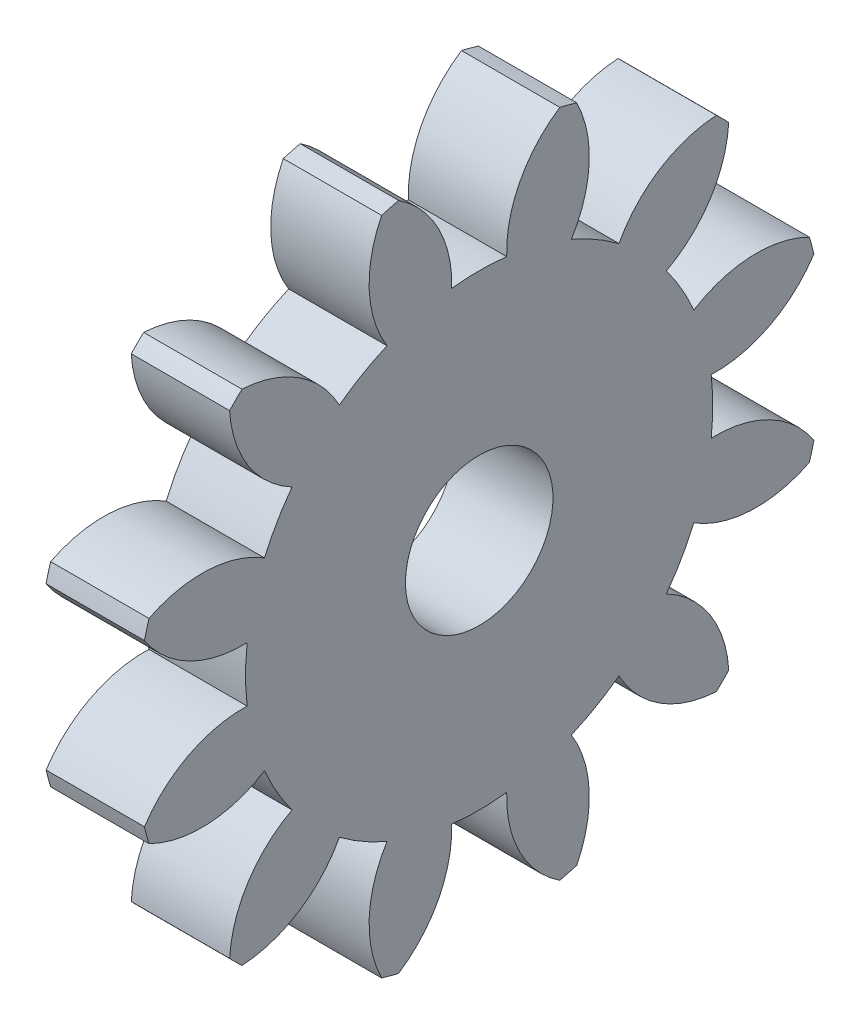
SolidWorks part; units mm, degrees
ref_plane "Plane1" through (0, 0, 0) normal (0, 0, 1) x (1, 0, 0)
ref_plane "Plane2" through (0, 0, 0) normal (0, 1, 0) x (1, 0, 0)
ref_plane "Plane3" through (0, 0, 0) normal (1, 0, 0) x (0, 0, -1)
sketch "HoldingSke" plane through (0, 0, 0) normal (0, 1, 0) x (1, 0, 0)
  line L0 (0, 0) -> (0.1534, -0.0354)
  line L1 (-15, 0) -> (100, 0) construction
  line L2 (0, 0) -> (-2.1039, 2.3779)
  line L3 (0, 0) -> (-11.863, 4.5341)
  line L4 (0, 0) -> (8.4473, 1.7955)
  line L5 (0, 0) -> (-23.7986, -8.8762)
  line L6 (0, 0) -> (-10.5278, -7.1032)
  line L7 (-2.1039, 2.3779) -> (3.3635, 27.1825)
  line L8 (-76.2, 54.61) -> (-73.66, 54.61)
  line L9 (-71.009, 38.7566) -> (-53.1078, 45.2721)
  line L10 (-76.2, 71.12) -> (104.1128, 71.12)
  line L11 (0, 0) -> (-12.7, 0)
  line L12 (-76.2, 101.6) -> (-75.9714, 101.6)
  line L13 (24.9733, 27.94) -> (52.9518, 28.4284)
  line L14 (24.9733, 27.94) -> (24.9746, 27.94)
  line L15 (24.9733, 27.94) -> (100.4006, 29.5858)
  line L16 (-63.627, -6.35) -> (-12.827, -6.35)
  circle A0 centre (0, 0) radius 9.525
  circle A1 centre (0, 0) radius 12.7
  circle A2 centre (0, 0) radius 12.7
  circle A3 centre (0, 0) radius 9.525
  dimension "Bore" = 19.05
  dimension "MBD" = 19.05
  dimension "T_dim" = 2.54
  dimension "Ap" = 20
  dimension "H" = 19.05
  dimension "Pitch_radius" = 180.3128
  dimension "Addendum_fac" = 1
  dimension "Dedendum_fac" = 1.25
  dimension "Clearance_fac" = 0.25
  dimension "Dedendum_add" = 0.0013
  dimension "Module" = 6.35
sketch "BasProSke" plane through (0, 0, 0) normal (0, 1, 0) x (1, 0, 0)
  line L0 (-10, 0) -> (60, 0) construction
  line L1 (0, 0) -> (0, 44.45)
  line L2 (0, 0) -> (12.7, 0)
  line L3 (12.7, 0) -> (12.7, 44.45)
  line L4 (12.7, 44.45) -> (0, 44.45)
revolve "Base-Revolve" add sketch "BasProSke" angle 360 about L0
sketch "TooCutSke" plane through (0, 0, 0) normal (1, 0, 0) x (0, 0, -1)
  line L1 (0, 0) -> (0, 107) construction
  line L2 (0, 0) -> (-5.3725, 37.7193) construction
  line L3 (0, 0) -> (-19.5794, 73.0714) construction
  line L4 (-5.3725, 37.7193) -> (-9.7897, 36.5357) construction
  arc A0 (3.5522, 29.9513) -> (-3.5522, 29.9513) centre (0, 0) ccw
  arc A1 (10.4397, 43.2328) -> (-10.4397, 43.2328) centre (0, 0) ccw
  circle A2 centre (0, 0) radius 38.1 construction
  circle A3 centre (0, 0) radius 35.8023 construction
  arc A4 (-3.5522, 29.9513) -> (-10.4397, 43.2328) centre (-18.7831, 30.4795) ccw
  arc A5 (10.4397, 43.2328) -> (3.5522, 29.9513) centre (18.7831, 30.4795) ccw
extrude "ToothCut" cut sketch "TooCutSke" along normal through all
fillet "Breaks" [suppressed] radius 0.127
fillet "RootFillets" [suppressed] radius 1.5888
pattern_circular "TeethCuts" count 12 every 30 about axis through (-10, 0, 0) along (1, 0, 0) of "ToothCut", "RootFillets", "Breaks"
sketch "HubNeaOneSke" plane through (0, 0, 0) normal (-1, 0, 0) x (0, 0, 1)
  circle A0 centre (0, 0) radius 12.7
extrude "HubNearOne" [suppressed] add sketch "HubNeaOneSke" along normal blind 12.7001
sketch "HubNeaBotSke" plane through (0, 0, 0) normal (-1, 0, 0) x (0, 0, 1)
  circle A0 centre (0, 0) radius 12.7
extrude "HubNearBoth" [suppressed] add sketch "HubNeaBotSke" along normal blind 6.35
ref_plane "FarPln" through (12.7, 0, 0) normal (1, 0, 0) x (0, 0, -1)
sketch "HubFarSke" plane through (12.7, 0, 0) normal (1, 0, 0) x (0, 0, -1)
  circle A0 centre (0, 0) radius 12.7
extrude "HubFar" [suppressed] add sketch "HubFarSke" along normal blind 6.35
sketch "BorSke" plane through (0, 0, 0) normal (1, 0, 0) x (0, 0, -1)
  circle A0 centre (0, 0) radius 9.525
  dimension "Diameter" = 19.05
extrude "Bore" cut sketch "BorSke" along normal mid plane 50.8001
sketch "KeySke" plane through (0, 0, 0) normal (1, 0, 0) x (0, 0, -1)
  line L0 (-3.175, 0) -> (-3.175, 12.065)
  line L1 (-3.175, 12.065) -> (3.175, 12.065)
  line L2 (3.175, 12.065) -> (3.175, 0)
  line L3 (0, 0) -> (0, 34) construction
  line L4 (-3.175, 0) -> (3.175, 0)
extrude "Keyway" [suppressed] cut sketch "KeySke" along normal mid plane 50.8001
pattern_circular "Keyway2" [suppressed] count 2 every 90 about axis through (-10, 0, 0) along (1, 0, 0)
equation "' \"Module@HoldingSke\" = 6.35"
equation "' \"Num_teeth@HoldingSke\" = 12"
equation "' \"Ap@HoldingSke\" =  20"
equation "' \"Ap@HoldingSke\" = 20"
equation "' \"Width@HoldingSke\" = 0.5 * 25.4"
equation "' \"Hub_dia@HoldingSke\"= 1 * 25.4"
equation "' \"Hub_dia@HoldingSke\" = 1 * 25.4"
equation "' \"Overall_len@HoldingSke\" = 1.0 * 25.4"
equation "' \"Bore@HoldingSke\" = 0.75 * 25.4"
equation "' \"T_dim@HoldingSke\" = 0.1 * 25.4"
equation "' \"Width@KeySke\" = 0.25 * 25.4"
equation "' \"Show_teeth@HoldingSke\" = 13"
equation "' \"Backlash@HoldingSke\" = 0.009 * 25.4"
equation "' \"Addendum_fac@HoldingSke\" = 1.0"
equation "' \"Dedendum_fac@HoldingSke\" = 1.25"
equation "' \"Dedendum_add@HoldingSke\" = 0.00005 * 25.4"
equation "' \"Clearance_fac@HoldingSke\" = 0.25"
equation "\"Pitch@HoldingSke\" = 1 / \"Module@HoldingSke\""
equation "\"Overcut_dia@TooCutSke\" = (\"Num_teeth@HoldingSke\" + 2 * \"Addendum_fac@HoldingSke\") / \"Pitch@HoldingSke\" + 0.002 * 25.4"
equation "\"Pitch_dia@TooCutSke\" = \"Num_teeth@HoldingSke\" / \"Pitch@HoldingSke\""
equation "\"Base_dia@TooCutSke\" = \"Num_teeth@HoldingSke\" / \"Pitch@HoldingSke\" * cos((\"Ap@HoldingSke\"  * 3.14159265 / 180))"
equation "\"Root_dia@TooCutSke\" = (\"Num_teeth@HoldingSke\" + 2) / \"Pitch@HoldingSke\" - 2 * (\"Addendum_fac@HoldingSke\" + \"Dedendum_fac@HoldingSke\") / \"Pitch@HoldingSke\" - \"Dedendum_add@HoldingSke\" * 2"
equation "\"Half_ang@TooCutSke\" = 180 / \"Num_teeth@HoldingSke\""
equation "\"Half_CT@TooCutSke\" = \"Num_teeth@HoldingSke\" / \"Pitch@HoldingSke\" * sin((3.14159265 / 2 / \"Num_teeth@HoldingSke\")) / 2 - 7 * \"Backlash@HoldingSke\" / 4"
equation "\"Flank_rad@TooCutSke\" = \"Num_teeth@HoldingSke\" / \"Pitch@HoldingSke\" / 5"
equation "\"Radius@RootFillets\" = \"Clearance_fac@HoldingSke\" / \"Pitch@HoldingSke\" + \"Dedendum_add@HoldingSke\""
equation "\"Break_rad@Breaks\" = 0.02 / \"Pitch@HoldingSke\""
equation "\"Thickness@HoldingSke\" = \"Width@HoldingSke\""
equation "\"OAL@HoldingSke\" = \"Thickness@HoldingSke\""
equation "\"MHD@HoldingSke\" = (\"Num_teeth@HoldingSke\" + 2) / \"Pitch@HoldingSke\" - 2 * (\"Addendum_fac@HoldingSke\" + \"Dedendum_fac@HoldingSke\")  / \"Pitch@HoldingSke\" - \"Dedendum_add@HoldingSke\" * 2"
equation "\"MBD@HoldingSke\" = (\"Num_teeth@HoldingSke\" + 2) / \"Pitch@HoldingSke\" - 2 * (\"Addendum_fac@HoldingSke\" + \"Dedendum_fac@HoldingSke\")  / \"Pitch@HoldingSke\" - \"Dedendum_add@HoldingSke\" * 2 - 0.002 * 25.4"
equation "\"MHD@HoldingSke\" = ((sgn( \"MHD@HoldingSke\" - \"Hub_dia@HoldingSke\" )-1)*( \"MHD@HoldingSke\" - \"Hub_dia@HoldingSke\" ))/-2+ \"Hub_dia@HoldingSke\""
equation "\"MBD@HoldingSke\" = ((sgn( \"MBD@HoldingSke\" - \"Bore@HoldingSke\" )-1)*( \"MBD@HoldingSke\" - \"Bore@HoldingSke\" ))/-2+ \"Bore@HoldingSke\""
equation "\"OAL@HoldingSke\" = ((sgn( \"OAL@HoldingSke\" - \"Overall_len@HoldingSke\" )+1)*( \"OAL@HoldingSke\" - \"Overall_len@HoldingSke\" ))/2 + \"Overall_len@HoldingSke\" + 0.000002 * 25.4"
equation "\"Num_teeth@TeethCuts\" = int( \"Show_teeth@HoldingSke\" ) + 1"
equation "\"Num_teeth@TeethCuts\" = ((sgn( \"Num_teeth@TeethCuts\" - \"Num_teeth@HoldingSke\" )-1)*( \"Num_teeth@TeethCuts\" - \"Num_teeth@HoldingSke\" ))/-2+ \"Num_teeth@HoldingSke\""
equation "\"Num_teeth@TeethCuts\" = ((sgn( \"Num_teeth@TeethCuts\" - 2.0)+1)*( \"Num_teeth@TeethCuts\" - 2.0))/2 +2.0"
equation "\"Angle@TeethCuts\" = 360.0 / \"Num_teeth@HoldingSke\""
equation "\"Diameter@BasProSke\" = (\"Num_teeth@HoldingSke\" + 2 * \"Addendum_fac@HoldingSke\") / \"Pitch@HoldingSke\""
equation "\"Thickness@BasProSke\"  = \"Thickness@HoldingSke\""
equation "' \"Fillet_rad@BasProSke\" =  \"Thickness@HoldingSke\" * 0.05"
equation "' \"Fillet_rad@BasProSke\" = \"Thickness@HoldingSke\" * 0.05"
equation "\"MHD@HoldingSke\" = ((sgn( \"MHD@HoldingSke\" - \"Root_dia@TooCutSke\" )-1)*( \"MHD@HoldingSke\" - \"Root_dia@TooCutSke\" ))/-2+ \"Root_dia@TooCutSke\""
equation "\"Diameter@HubNeaOneSke\" = \"MHD@HoldingSke\""
equation "\"Length@HubNearOne\" = \"OAL@HoldingSke\" - \"Thickness@BasProSke\""
equation "\"Diameter@HubNeaBotSke\" = \"MHD@HoldingSke\""
equation "\"Length@HubNearBoth\" = ( \"OAL@HoldingSke\" - \"Thickness@BasProSke\" ) / 2.0"
equation "\"Thickness@FarPln\" = \"Thickness@BasProSke\""
equation "\"Diameter@HubFarSke\" = \"MHD@HoldingSke\""
equation "\"Length@HubFar\" = ( \"OAL@HoldingSke\" - \"Thickness@BasProSke\" ) / 2.0"
equation "\"Diameter@BorSke\" = \"MBD@HoldingSke\""
equation "\"D1@Bore\" = \"OAL@HoldingSke\" * 2.0"
equation "\"D1@Keyway\" = \"OAL@HoldingSke\" * 2.0"
equation "\"Offset@KeySke\" = \"T_dim@HoldingSke\" + \"MBD@HoldingSke\" / 2.0"
